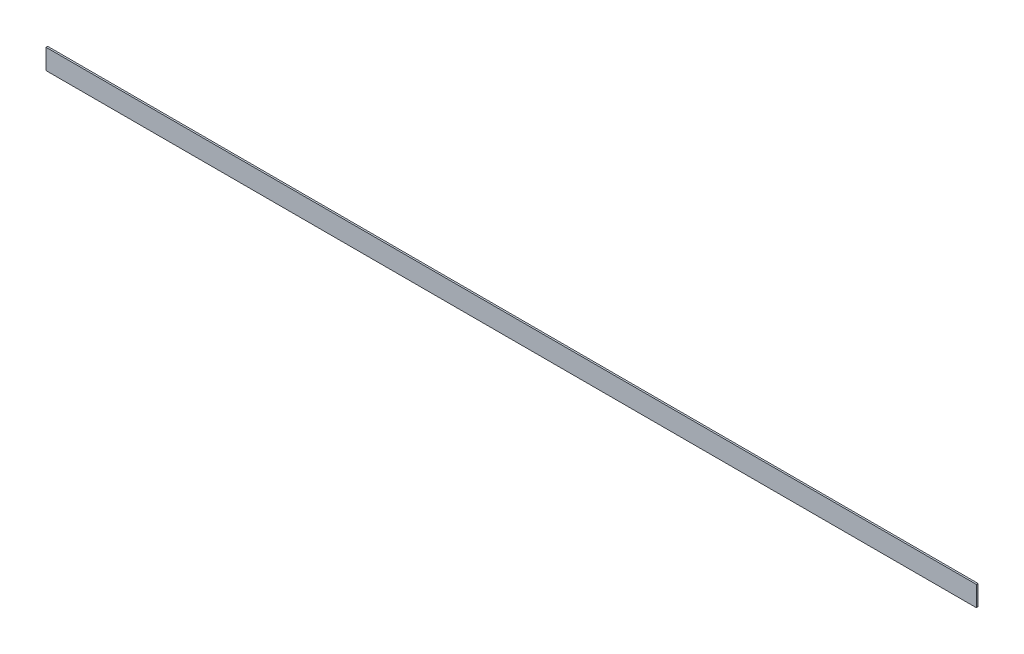
SolidWorks part; units mm, degrees
material "PVC 0.007 Plasticized"
ref_plane "Front Plane" through (0, 0, 0) normal (0, 0, 1) x (1, 0, 0)
ref_plane "Top Plane" through (0, 0, 0) normal (0, 1, 0) x (1, 0, 0)
ref_plane "Right Plane" through (0, 0, 0) normal (1, 0, 0) x (0, 0, -1)
sketch "Sketch1" plane through (0, 0, 0) normal (1, 0, 0) x (0, 0, -1)
  line L1 (-3.175, -38.1) -> (3.175, -38.1)
  line L2 (-3.175, -38.1) -> (-3.175, 38.1)
  line L3 (-3.175, 38.1) -> (3.175, 38.1)
  line L4 (3.175, -38.1) -> (3.175, 38.1)
  line L5 (-3.175, -38.1) -> (3.175, 38.1) construction
  line L6 (-3.175, 38.1) -> (3.175, -38.1) construction
  point P0 (0, 0)
  dimension "D1" = 76.2
  dimension "D2" = 6.35
extrude "Boss-Extrude1" add sketch "Sketch1" along normal blind 3505.2
equation "\"D2@Sketch1\"=1in/4"
